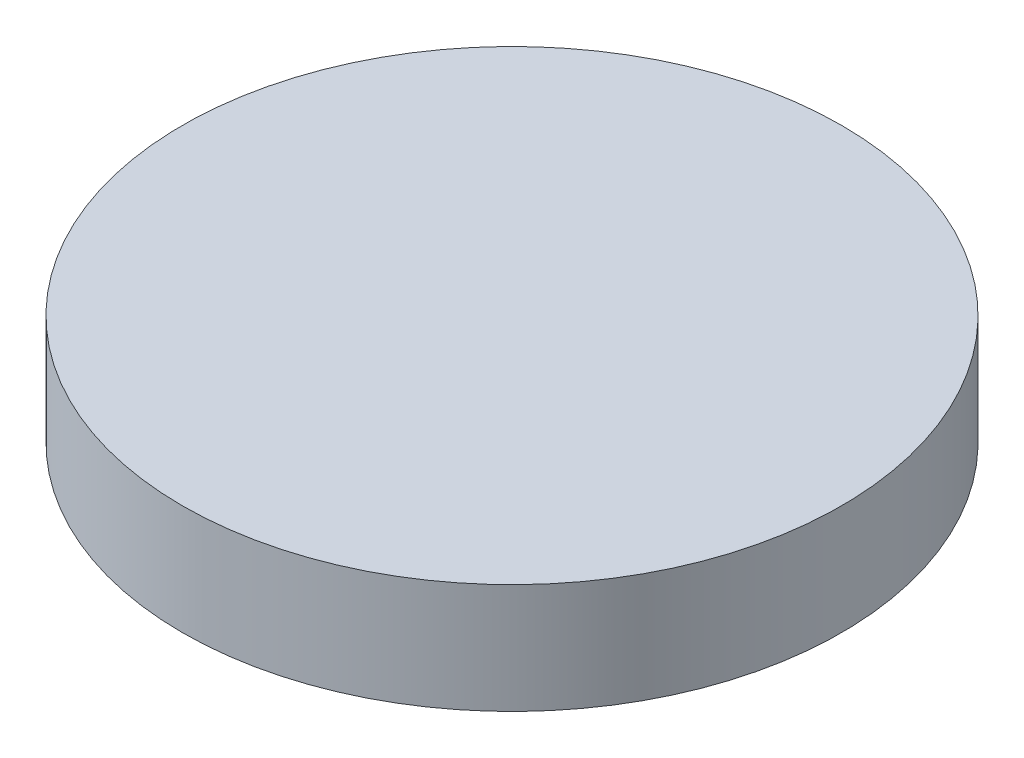
SolidWorks part; units mm, degrees
ref_plane "Front Plane" through (0, 0, 0) normal (0, 0, 1) x (1, 0, 0)
ref_plane "Top Plane" through (0, 0, 0) normal (0, 1, 0) x (1, 0, 0)
ref_plane "Right Plane" through (0, 0, 0) normal (1, 0, 0) x (0, 0, -1)
sketch "Wheel" plane through (0, 0, 0) normal (0, 1, 0) x (1, 0, 0)
  circle A0 centre (0, 0) radius 30
  dimension "D1" = 60
extrude "Extrude wheel" add sketch "Wheel" along normal blind 10
